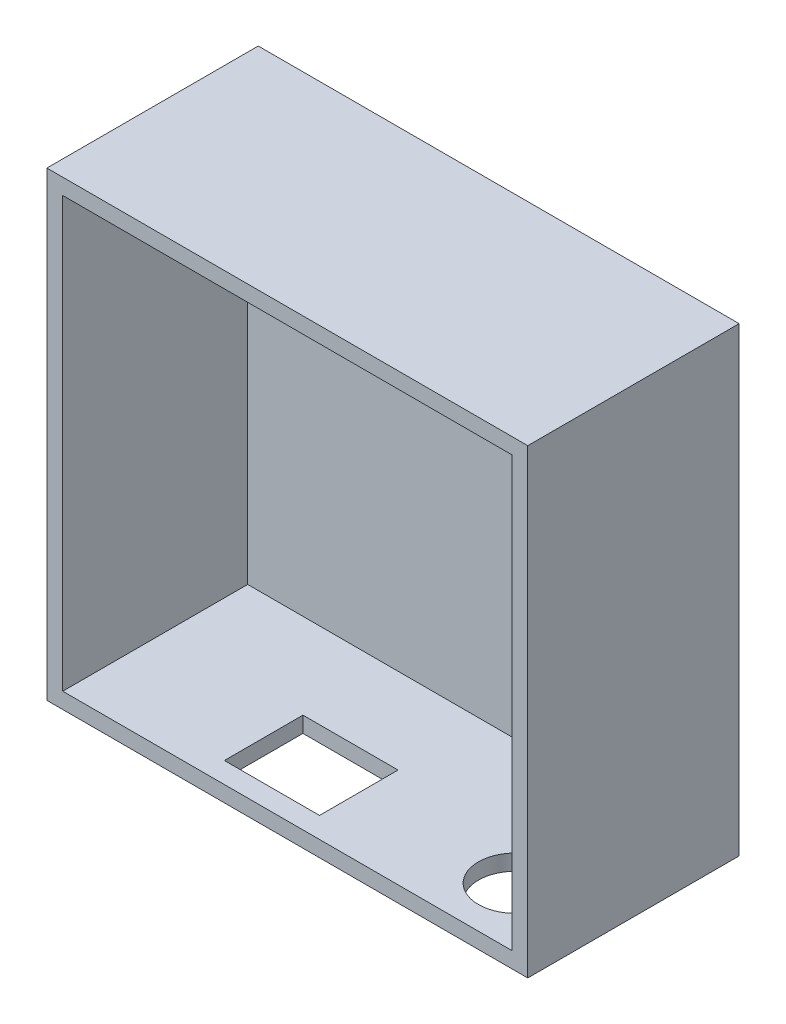
SolidWorks part; units mm, degrees
ref_plane "Front Plane" through (0, 0, 0) normal (0, 0, 1) x (1, 0, 0)
ref_plane "Top Plane" through (0, 0, 0) normal (0, 1, 0) x (1, 0, 0)
ref_plane "Right Plane" through (0, 0, 0) normal (1, 0, 0) x (0, 0, -1)
sketch "Sketch2" plane through (0, 0, 0) normal (0, 0, 1) x (1, 0, 0)
  line L0 (75.184, 76.2) -> (5.464, 76.2) construction
  line L1 (-2.1835, 79.2) -> (82.8165, 79.2)
  line L2 (-2.1835, 79.2) -> (-2.1835, -2.0443)
  line L3 (-2.1835, -2.0443) -> (82.8165, -2.0443)
  line L4 (82.8165, 79.2) -> (82.8165, -2.0443)
  point P6 (0, 0)
  dimension "D1" = 3
  dimension "D2" = 85
sketch "Sketch3" plane through (0, 0, 0) normal (0, 0, 1) x (1, 0, 0)
  line L0 (-2.1835, 79.2) -> (82.8165, 79.2) construction
  line L1 (-5.1835, 82.2) -> (85.8165, 82.2)
  line L2 (-5.1835, 82.2) -> (-5.1835, -5.0443)
  line L3 (-5.1835, -5.0443) -> (85.8165, -5.0443)
  line L4 (85.8165, 82.2) -> (85.8165, -5.0443)
  line L5 (-2.1835, -2.0443) -> (82.8165, -2.0443) construction
  line L6 (82.8165, 79.2) -> (82.8165, -2.0443) construction
  line L7 (-2.1835, 79.2) -> (-2.1835, -2.0443) construction
  dimension "D1" = 3
  dimension "D2" = 3
  dimension "D3" = 3
  dimension "D4" = 3
extrude "Boss-Extrude1" add sketch "Sketch3" along normal blind 35 and the other way blind 5
extrude "Cut-Extrude1" cut sketch "Sketch2" along normal blind 41
sketch "Sketch5" plane through (0, -5.0443, 0) normal (0, -1, 0) x (1, 0, 0)
  line L0 (41.964, 30.5585) -> (24.964, 30.5585) construction
  line L1 (24.464, 16.1885) -> (42.464, 16.1885)
  line L2 (24.464, 16.1885) -> (24.464, 31.0585)
  line L3 (24.464, 31.0585) -> (42.464, 31.0585)
  line L4 (42.464, 16.1885) -> (42.464, 31.0585)
  line L5 (24.464, 16.1885) -> (42.464, 31.0585) construction
  line L6 (24.464, 31.0585) -> (42.464, 16.1885) construction
  line L7 (41.964, 16.6885) -> (24.964, 16.6885) construction
  line L8 (41.964, 16.6885) -> (41.964, 30.5585) construction
  line L9 (24.964, 16.6885) -> (24.964, 30.5585) construction
  circle A0 centre (72.1076, 23.6235) radius 7
  point P0 (33.464, 23.6235)
  point P15 (72.1076, 23.6235)
  dimension "D1" = 0.5
  dimension "D2" = 0.5
  dimension "D3" = 0.5
  dimension "D4" = 0.5
extrude "Cut-Extrude2" cut sketch "Sketch5" against normal up to next
